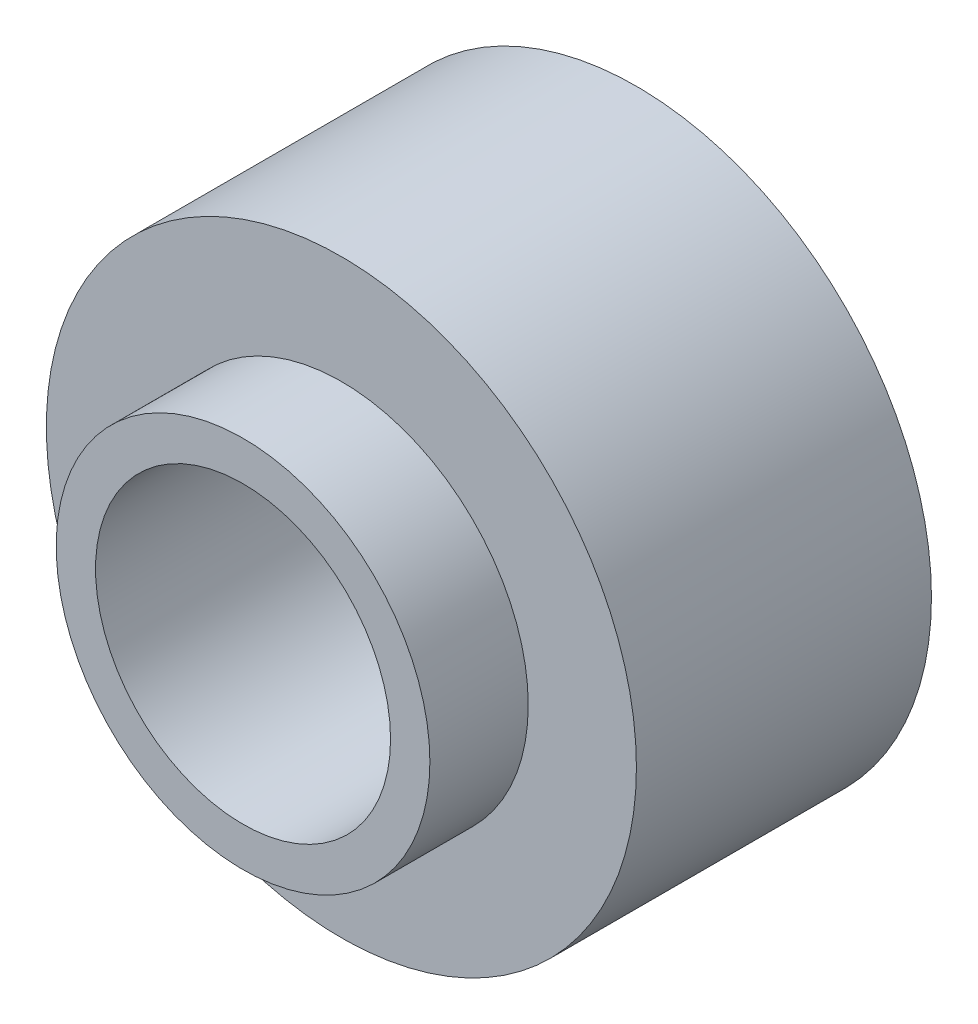
SolidWorks part; units mm, degrees
ref_plane "Front Plane" through (0, 0, 0) normal (0, 0, 1) x (1, 0, 0)
ref_plane "Top Plane" through (0, 0, 0) normal (0, 1, 0) x (1, 0, 0)
ref_plane "Right Plane" through (0, 0, 0) normal (1, 0, 0) x (0, 0, -1)
sketch "Sketch2" plane through (0, 0, 0) normal (0, 0, 1) x (1, 0, 0)
  circle A0 centre (0, 0) radius 9.525
  circle A1 centre (0, 0) radius 4.7625
extrude "Boss-Extrude1" add sketch "Sketch2" along normal blind 12.7
sketch "Sketch3" plane through (0, 0, 12.7) normal (0, 0, 1) x (1, 0, 0)
  circle A0 centre (0, 0) radius 6.0325
  circle A1 centre (0, 0) radius 9.525
extrude "Cut-Extrude1" cut sketch "Sketch3" against normal blind 3.175
